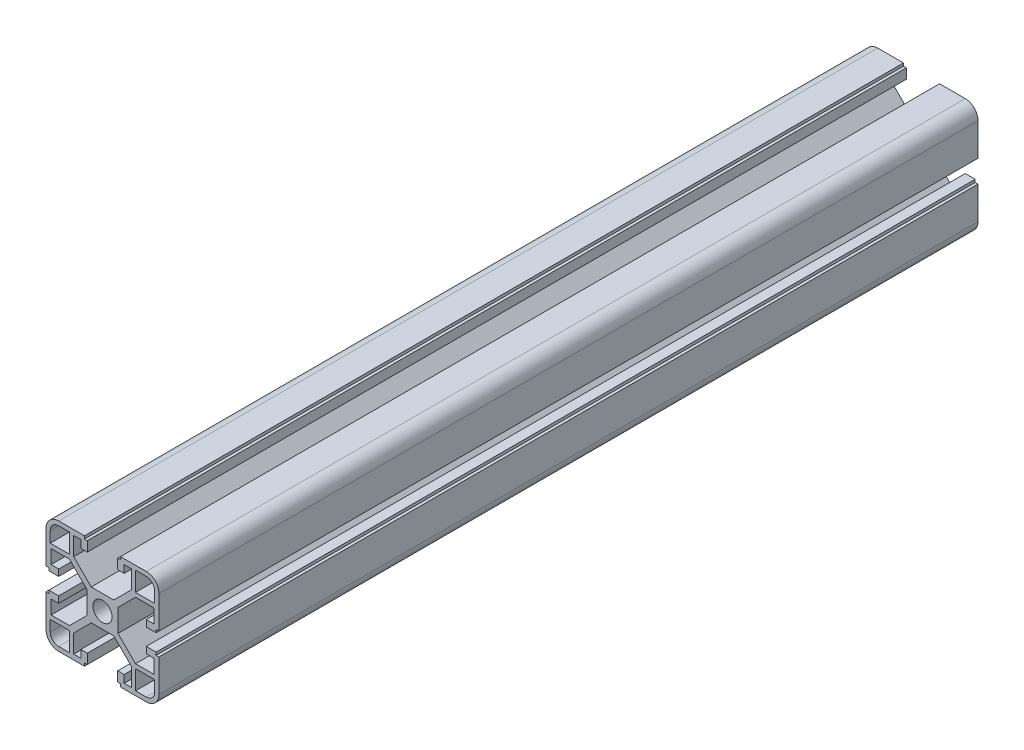
SolidWorks part; units mm, degrees
material "6061-T6 (SS)"
ref_plane "Front Plane" through (0, 0, 0) normal (0, 0, 1) x (1, 0, 0)
ref_plane "Top Plane" through (0, 0, 0) normal (0, 1, 0) x (1, 0, 0)
ref_plane "Right Plane" through (0, 0, 0) normal (1, 0, 0) x (0, 0, -1)
sketch "Sketch1" plane through (0, 0, 0) normal (0, 0, 1) x (1, 0, 0)
  line L0 (3.4, 0) -> (5.5, 0)
  line L1 (10.19, 11.69) -> (4, 5.5)
  line L2 (11.69, 10.19) -> (5.5, 4)
  line L3 (18.2, 10.19) -> (11.69, 10.19)
  line L4 (18.2, 10.19) -> (18.2, 5.2656)
  line L5 (18.2, 5.2656) -> (15.5, 5.2656)
  line L6 (15.5, 5.2656) -> (15.5, 2.9656)
  line L7 (15.5, 2.9656) -> (19, 2.9656)
  line L8 (19, 2.9656) -> (19, 3.9656)
  line L9 (19, 3.9656) -> (20, 3.9656)
  line L10 (20, 3.9656) -> (20, 15.5)
  line L11 (15.5, 20) -> (6.3853, 20)
  line L12 (18.5, 11.69) -> (18.5, 15.5)
  line L13 (15.5, 18.5) -> (11.69, 18.5)
  line L14 (11.69, 11.69) -> (11.69, 18.5)
  line L15 (0, 3.4) -> (0, 5.5)
  line L16 (4, 5.5) -> (0, 5.5)
  line L17 (6.3853, 20) -> (6.3853, 19)
  line L18 (5.5, 0) -> (5.5, 4)
  line L19 (6.3853, 19) -> (5.3853, 19)
  line L20 (5.3853, 19) -> (5.3853, 15.5)
  line L21 (5.3853, 15.5) -> (7.6853, 15.5)
  line L22 (10.19, 11.69) -> (10.19, 18.2)
  line L23 (11.69, 11.69) -> (18.5, 11.69)
  line L24 (7.6853, 18.2) -> (7.6853, 15.5)
  line L25 (10.19, 18.2) -> (7.6853, 18.2)
  arc A0 (20, 15.5) -> (15.5, 20) centre (15.5, 15.5) ccw
  arc A1 (18.5, 15.5) -> (15.5, 18.5) centre (15.5, 15.5) ccw
  arc A2 (3.4, 0) -> (0, 3.4) centre (0, 0) ccw
  dimension "D3" = 4.5
  dimension "D18" = 1.5
  dimension "D9" = 3.4
  dimension "D20" = 1.8
  dimension "D25" = 3
  dimension "D1" = 5.5
  dimension "D2" = 1.5
  dimension "D4" = 14.5
  dimension "D5" = 1.5
  dimension "D6" = 2.1
  dimension "D7" = 2.3
  dimension "D8" = 1.8
  dimension "D10" = 6.81
  dimension "D11" = 2.1
  dimension "D12" = 1
  dimension "D13" = 4.5
  dimension "D14" = 45
  dimension "D15" = 14.5
  dimension "D16" = 1
  dimension "D17" = 1.5
  dimension "D19" = 6.81
  dimension "D21" = 4.5
  dimension "D22" = 2.3
  dimension "D23" = 1
  dimension "D24" = 1
  dimension "D26" = 8.754
  dimension "D27" = 8.754
  dimension "D28" = 4.9244
  dimension "D29" = 2.5047
extrude "Boss-Extrude1" add sketch "Sketch1" along normal blind 290
mirror "Mirror1" about plane through (0, 0, 0) normal (0, 1, 0) of "Boss-Extrude1"
mirror "Mirror2" about plane through (0, 0, 0) normal (1, 0, 0) of "Boss-Extrude1"
mirror "Mirror3" about plane through (0, 0, 0) normal (0, 1, 0) of "Mirror2"
